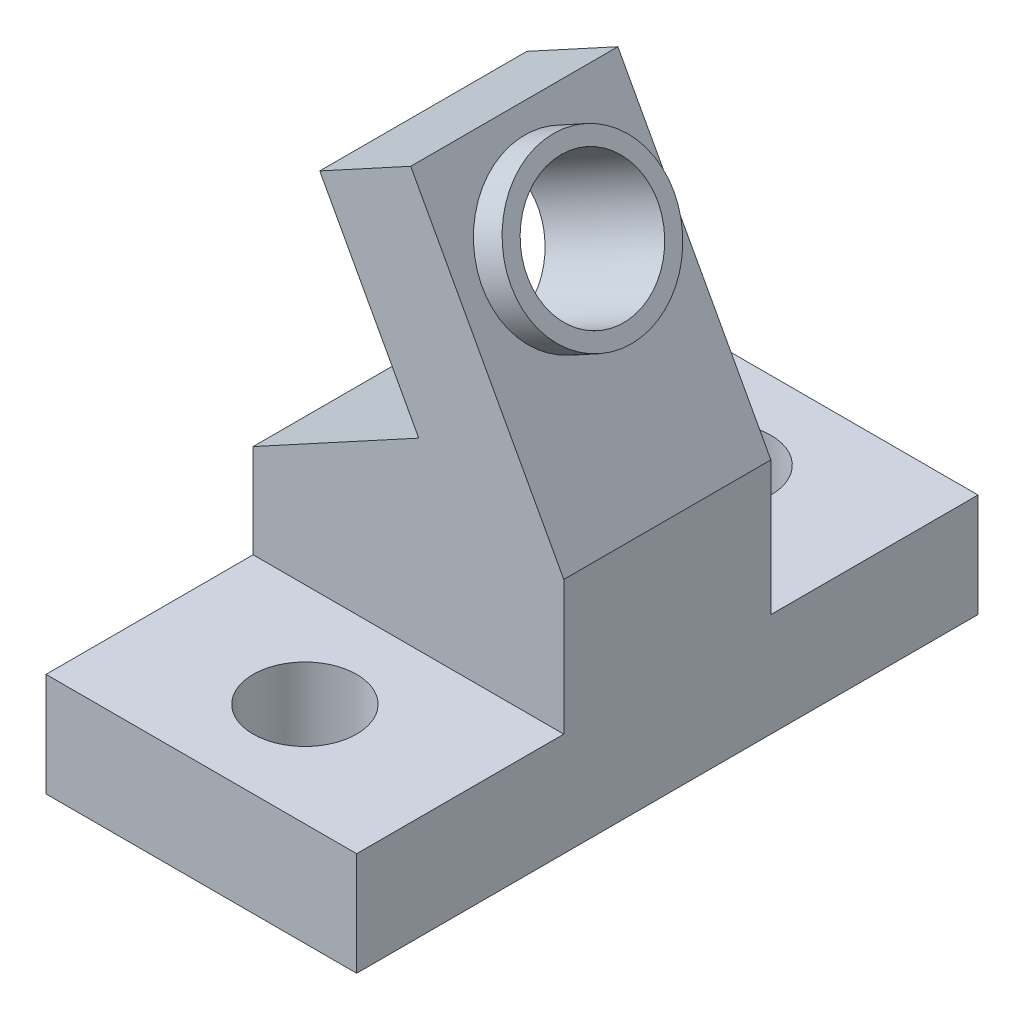
SolidWorks part; units mm, degrees
ref_plane "Front Plane" through (0, 0, 0) normal (0, 0, 1) x (1, 0, 0)
ref_plane "Top Plane" through (0, 0, 0) normal (0, 1, 0) x (1, 0, 0)
ref_plane "Right Plane" through (0, 0, 0) normal (1, 0, 0) x (0, 0, -1)
sketch "Sketch1" plane through (0, 0, 0) normal (0, 0, 1) x (1, 0, 0)
  line L0 (-12.7, 0) -> (12.7, 0)
  line L1 (12.7, 0) -> (12.7, 2.8936)
  line L2 (12.7, 2.8936) -> (-12.7, 49.5774)
  line L3 (-12.7, 49.5774) -> (-12.7, 0)
  line L4 (12.7, 2.8936) -> (-12.7, 2.8936) construction
  line L5 (0, 26.2355) -> (5.299, 29.1186) construction
  line L6 (-2.2881, 43.0632) -> (12.886, 15.174) construction
  point P6 (0, 0)
  point P11 (5.299, 29.1186)
  dimension "D1" = 25.4
  dimension "D2" = 61.45
  dimension "D3" = 6.0325
  dimension "D4" = 31.75
  dimension "D5" = 15.174
extrude "Boss-Extrude1" add sketch "Sketch1" along normal blind 12.7
sketch "Sketch2" plane through (11.0139, 5.9925, 0) normal (0.8784, 0.4779, 0) x (0.4779, -0.8784, 0)
  line L0 (-49.6184, -6.35) -> (3.5279, -6.35) construction
  line L1 (-49.6184, -12.7) -> (-49.6184, 0) construction
  line L2 (3.5279, -12.7) -> (3.5279, 0) construction
  circle A0 centre (-23.0453, -6.35) radius 4
  dimension "D1" = 8
sketch "Sketch3" plane through (0, 0, 12.7) normal (0, 0, 1) x (1, 0, 0)
  line L0 (-8.89, 29.2882) -> (-2.2657, 17.1131)
  line L1 (-2.2657, 17.1131) -> (-2.2657, 10.7631)
  line L2 (-2.2657, 10.7631) -> (-8.89, 10.7631)
  line L3 (-8.89, 10.7631) -> (-8.89, 29.2882)
  line L4 (-12.7, 49.5774) -> (12.7, 2.8936) construction
  line L5 (0, 26.2355) -> (-0.6283, 25.8936) construction
  line L6 (12.7, 2.8936) -> (-12.7, 49.5774) construction
  line L7 (-5.5778, 23.2007) -> (1.5436, 27.0753) construction
  line L8 (-12.7, 49.5774) -> (-12.7, 0) construction
  dimension "D1" = 6.35
  dimension "D2" = 3.81
  dimension "D3" = 6.35
extrude "Cut-Extrude3" cut sketch "Sketch2" against normal up to next
sketch "Sketch4" plane through (11.0139, 5.9925, 0) normal (0.8784, 0.4779, 0) x (0.4779, -0.8784, 0)
  circle A0 centre (-23.0453, -6.35) radius 5
  circle A1 centre (-23.0453, -6.35) radius 4 construction
  circle A2 centre (-23.0453, -6.35) radius 4
  dimension "D1" = 10
extrude "Boss-Extrude2" add sketch "Sketch4" along normal blind 2
sketch "Sketch5" plane through (0, 0, 12.7) normal (0, 0, 1) x (1, 0, 0)
  line L0 (-12.7, 49.5774) -> (-12.7, 0) construction
  line L1 (-12.7, 36.8774) -> (-5.7901, 36.8774)
  line L2 (-12.7, 36.8774) -> (-12.7, 49.5774)
  line L3 (-12.7, 49.5774) -> (-5.7901, 49.5774)
  line L4 (-5.7901, 36.8774) -> (-5.7901, 49.5774)
  line L5 (12.7, 2.8936) -> (-12.7, 49.5774) construction
  dimension "D1" = 12.7
extrude "Cut-Extrude4" cut sketch "Sketch5" against normal up to next
sketch "Sketch7" plane through (0, 0, 12.7) normal (0, 0, 1) x (1, 0, 0)
  line L5 (-12.7, 36.8774) -> (-12.7, 0) construction
  line L6 (-12.7, 6.35) -> (6.35, 6.35)
  line L7 (-12.7, 6.35) -> (-12.7, 0)
  line L8 (-12.7, 0) -> (6.35, 0)
  line L9 (6.35, 6.35) -> (6.35, 0)
  line L10 (-12.7, 0) -> (12.7, 0) construction
  dimension "D1" = 6.35
  dimension "D2" = 19.05
extrude "Boss-Extrude3" add sketch "Sketch7" along normal blind 12.7
sketch "Sketch8" plane through (0, 0, 12.7) normal (0, 0, 1) x (1, 0, 0)
  line L0 (-8.6127, 28.7785) -> (-2.543, 17.6228)
  line L1 (-2.543, 17.6228) -> (-12.7, 12.0965)
  line L2 (-12.7, 36.8774) -> (-12.7, 6.35) construction
  line L3 (-12.7, 12.0965) -> (-12.7, 26.5546)
  line L4 (-12.7, 26.5546) -> (-8.6127, 28.7785)
  line L6 (-5.5778, 23.2007) -> (1.5436, 27.0753) construction
  line L7 (12.7, 2.8936) -> (-5.7901, 36.8774) construction
  point P9 (-5.5778, 23.2007)
  dimension "D1" = 12.7
  dimension "D2" = 6.35
extrude "Cut-Extrude5" cut sketch "Sketch8" against normal blind 12.7
sketch "Sketch9" plane through (0, 6.35, 0) normal (0, 1, 0) x (1, 0, 0)
  line L0 (-12.7, -19.05) -> (6.35, -19.05) construction
  line L1 (-12.7, -25.4) -> (-12.7, -12.7) construction
  line L2 (6.35, -25.4) -> (6.35, -12.7) construction
  circle A0 centre (-3.175, -19.05) radius 3.175
  point P10 (-3.175, -19.05)
  point P12 (6.35, -19.05)
  dimension "D1" = 6.35
extrude "Cut-Extrude6" cut sketch "Sketch9" against normal blind 12.7
ref_plane "Plane2" through (0, 0, 6.35) normal (0, 0, 1) x (1, 0, 0)
mirror "Mirror1" about plane through (0, 0, 6.35) normal (0, 0, 1) of "Cut-Extrude6", "Boss-Extrude3"
sketch "Sketch11" plane through (0, 0, 12.7) normal (0, 0, 1) x (1, 0, 0)
  line L0 (-12.7, 26.5546) -> (-3.0348, 31.8133)
  line L1 (12.7, 2.8936) -> (-5.7901, 36.8774) construction
  line L2 (-8.6127, 28.7785) -> (-12.7, 26.5546) construction
  line L3 (-12.7, 26.5546) -> (-12.7, 36.8774)
  line L4 (-12.7, 36.8774) -> (-5.7901, 36.8774)
  line L5 (-5.7901, 36.8774) -> (-3.0348, 31.8133)
  line L6 (12.7, 0) -> (12.7, 2.8936) construction
  line L7 (6.35, 0) -> (12.7, 0)
  line L8 (6.35, 0) -> (6.35, 14.5645)
  line L9 (6.35, 14.5645) -> (12.7, 14.5645)
  line L10 (12.7, 0) -> (12.7, 14.5645)
extrude "Cut-Extrude7" cut sketch "Sketch11" against normal blind 12.7
